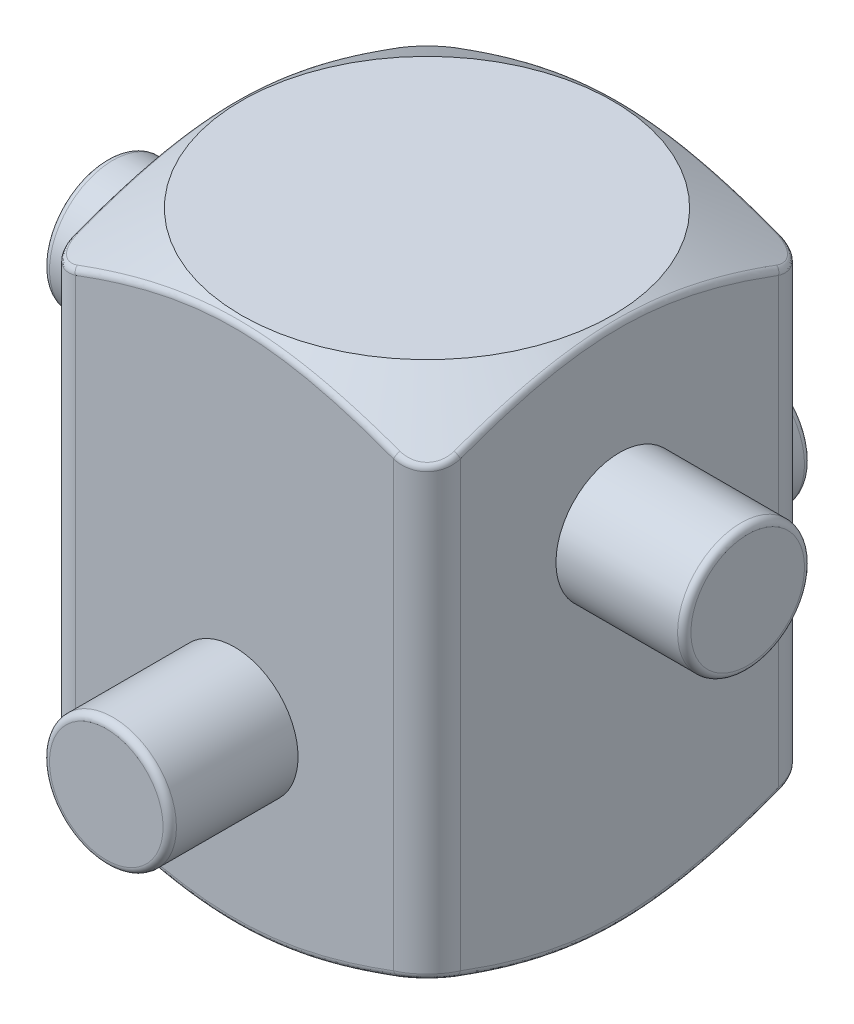
SolidWorks part; units mm, degrees
material "Rubber"
ref_plane "Front Plane" through (0, 0, 0) normal (0, 0, 1) x (1, 0, 0)
ref_plane "Top Plane" through (0, 0, 0) normal (0, 1, 0) x (1, 0, 0)
ref_plane "Right Plane" through (0, 0, 0) normal (1, 0, 0) x (0, 0, -1)
sketch "Sketch1" plane through (0, 0, 0) normal (0, 1, 0) x (1, 0, 0)
  line L1 (7.2, -7.2) -> (-7.2, -7.2)
  line L2 (7.2, -7.2) -> (7.2, 7.2)
  line L3 (7.2, 7.2) -> (-7.2, 7.2)
  line L4 (-7.2, -7.2) -> (-7.2, 7.2)
  line L5 (7.2, -7.2) -> (-7.2, 7.2) construction
  line L6 (7.2, 7.2) -> (-7.2, -7.2) construction
  point P0 (0, 0)
  dimension "D1" = 14.4
extrude "Boss-Extrude1" add sketch "Sketch1" along normal blind 19.7
ref_axis "Axis1" through (0, 20.685, 0) along (0, -1, 0)
sketch "Sketch2" plane through (0, 0, 0) normal (0, 0, 1) x (1, 0, 0)
  line L0 (-6.95, 19.7) -> (-16.09, 19.7)
  line L1 (-7.2, 19.7) -> (7.2, 19.7) construction
  line L2 (-16.09, 19.7) -> (-16.09, 0)
  line L3 (-16.09, 0) -> (-6.95, 0)
  line L4 (-7.2, 0) -> (7.2, 0) construction
  line L5 (-6.95, 0) -> (-13.55, 3.8105)
  line L6 (-13.55, 3.8105) -> (-13.55, 15.8895)
  line L7 (-13.55, 15.8895) -> (-6.95, 19.7)
  line L8 (-7.2, 19.7) -> (-7.2, 0) construction
  dimension "D1" = 0.25
  dimension "D2" = 0.25
  dimension "D3" = 30
  dimension "D4" = 30
  dimension "D5" = 2.54
  dimension "D6" = 6.35
revolve "Cut-Revolve1" cut sketch "Sketch2" angle 360 about axis through (0, 20.685, 0) along (0, -1, 0)
sketch "Sketch3" plane through (0, 0, 0) normal (0, 0, 1) x (1, 0, 0)
  line L0 (0, 20.685) -> (0, -0.985) construction
  circle A0 centre (0, 6.7) radius 2.375
  dimension "D1" = 4.75
  dimension "D2" = 6.7
extrude "Boss-Extrude2" add sketch "Sketch3" along normal mid plane 24
sketch "Sketch4" plane through (0, 0, 0) normal (1, 0, 0) x (0, 0, -1)
  line L0 (0, 20.685) -> (0, -0.985) construction
  line L1 (6.95, 19.7) -> (-6.95, 19.7) construction
  circle A0 centre (0, 13) radius 2.375
  dimension "D1" = 4.75
  dimension "D2" = 6.7
extrude "Boss-Extrude3" add sketch "Sketch4" along normal mid plane 24
fillet "Fillet1" radius 1.25 4 edges at (7.2, 9.85, -7.2) (7.2, 9.85, 7.2) (-7.2, 9.85, 7.2) (-7.2, 9.85, -7.2)
fillet "Fillet2" radius 0.25 20 edges at (6.9494, 1.561, 6.7009) (-0.815, 0.1709, 7.2) (-6.7009, 1.561, 6.9494) (-7.2, 0.1709, -0.815) (-6.9494, 1.561, -6.7009) (-0.815, 0.1709, -7.2) (6.7009, 1.561, -6.9494) (6.7009, 18.139, 6.9494) (7.2, 19.5291, -0.815) (6.9494, 18.139, -6.7009) (-0.815, 19.5291, -7.2) (-6.7009, 18.139, -6.9494) (-7.2, 19.5291, -0.815) (-6.9494, 18.139, 6.7009) (2.375, 6.7, 12) (2.375, 6.7, -12) (-12, 13, -2.375) (7.2, 0.1709, -0.815) (12, 13, -2.375) (-0.815, 19.5291, 7.2)
